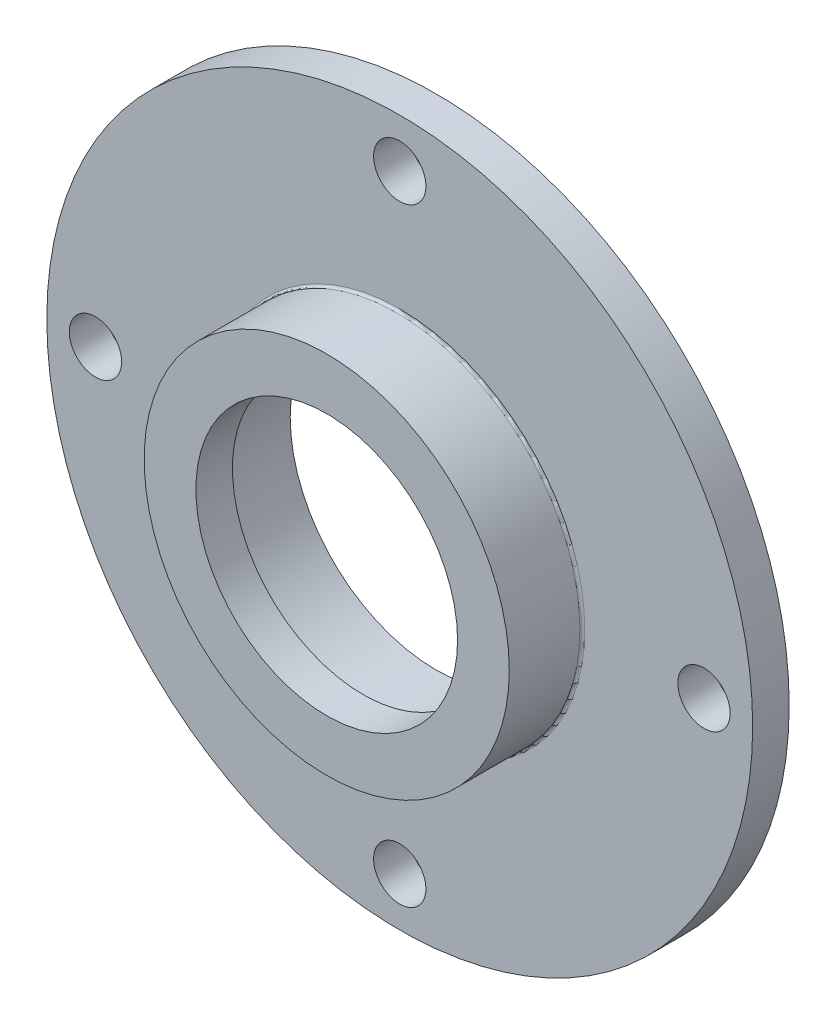
SolidWorks part; units mm, degrees
material "1060 Alloy"
ref_plane "Front Plane" through (0, 0, 0) normal (0, 0, 1) x (1, 0, 0)
ref_plane "Top Plane" through (0, 0, 0) normal (0, 1, 0) x (1, 0, 0)
ref_plane "Right Plane" through (0, 0, 0) normal (1, 0, 0) x (0, 0, -1)
sketch "Sketch1" plane through (0, 0, 0) normal (0, 0, 1) x (1, 0, 0)
  circle A0 centre (0, 0) radius 29
  circle A1 centre (0, 0) radius 12
  dimension "D1" = 58
  dimension "D2" = 24
extrude "Boss-Extrude1" add sketch "Sketch1" along normal blind 3
sketch "Sketch2" plane through (0, 0, 3) normal (0, 0, 1) x (1, 0, 0)
  circle A0 centre (0, 0) radius 12
  circle A1 centre (0, 0) radius 15
  dimension "D1" = 30
  dimension "D2" = 24
extrude "Boss-Extrude2" add sketch "Sketch2" along normal blind 6
sketch "Sketch3" plane through (0, 0, 9) normal (0, 0, 1) x (1, 0, 0)
  circle A0 centre (0, 0) radius 15
  circle A1 centre (0, 0) radius 10.75
  dimension "D1" = 21.5
  dimension "D2" = 30
extrude "Boss-Extrude3" add sketch "Sketch3" against normal blind 3
hole_wizard "M4 Clearance Hole1" positions "Sketch7" profile "Sketch6" hole size "M4" standard "ISO" end condition through all
sketch "Sketch7" plane through (0, 0, 3) normal (0, 0, 1) x (1, 0, 0)
  point P0 (0, 25)
  point P9 (25, 0)
  point P10 (0, -25)
  point P11 (-25, 0)
  point P12 (0, 0)
  dimension "D1" = 25
  dimension "D2" = 4
sketch "Sketch6" plane through (0, 25, 3) normal (1, 0, 0) x (0, -1, 0)
  line L0 (0, 0) -> (0, 3)
  line L1 (0, 3) -> (2.15, 3)
  line L2 (2.15, 3) -> (2.15, 0)
  line L5 (2.15, 0) -> (0, 0)
  line L11 (0, -6.35) -> (0, 107.95) construction
  dimension "Thru Hole Dia." = 4.3
  dimension "Thru Hole Depth" = 3
fillet "Fillet1" radius 0.2 2 edges at (12, 0, 6) (15, 0, 3)
